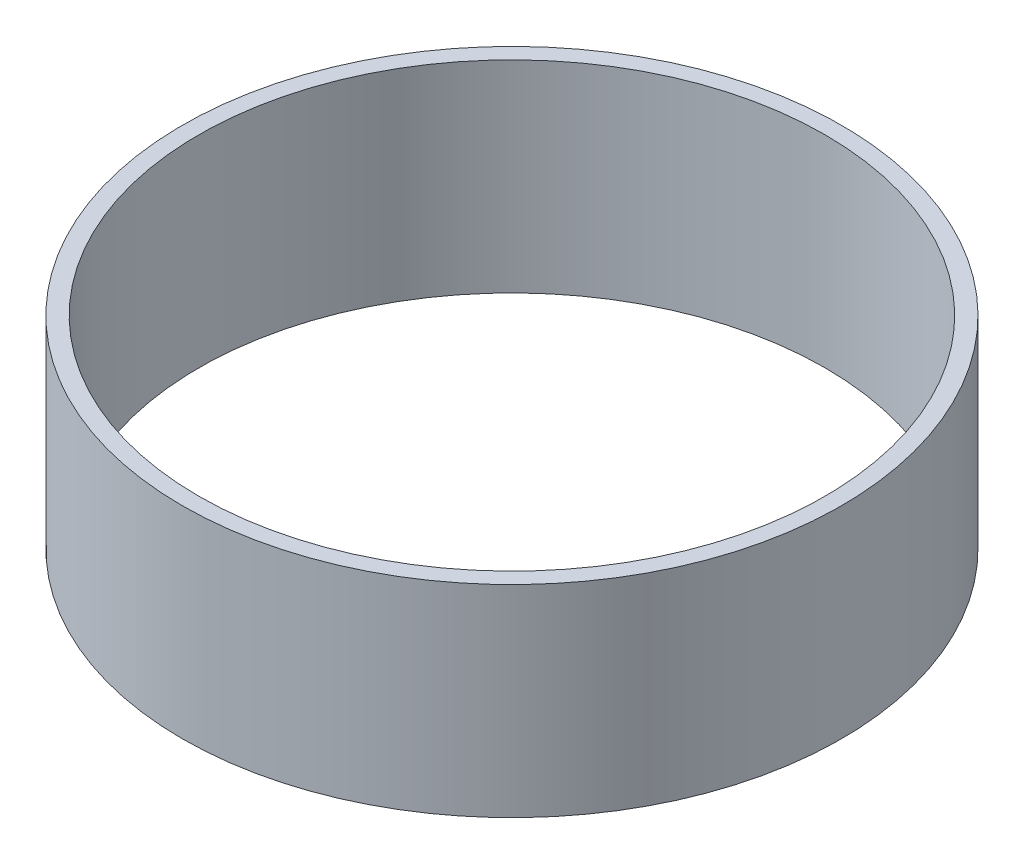
SolidWorks part; units mm, degrees
material "1060 合金"
ref_plane "前视基准面" through (0, 0, 0) normal (0, 0, 1) x (1, 0, 0)
ref_plane "上视基准面" through (0, 0, 0) normal (0, 1, 0) x (1, 0, 0)
ref_plane "右视基准面" through (0, 0, 0) normal (1, 0, 0) x (0, 0, -1)
other "Configuration Table"
sketch "草图1" plane through (0, 0, 0) normal (0, 1, 0) x (1, 0, 0)
  circle A0 centre (0, 0) radius 40
  circle A1 centre (0, 0) radius 38
extrude "凸台-拉伸1" add sketch "草图1" along normal blind 24.5
